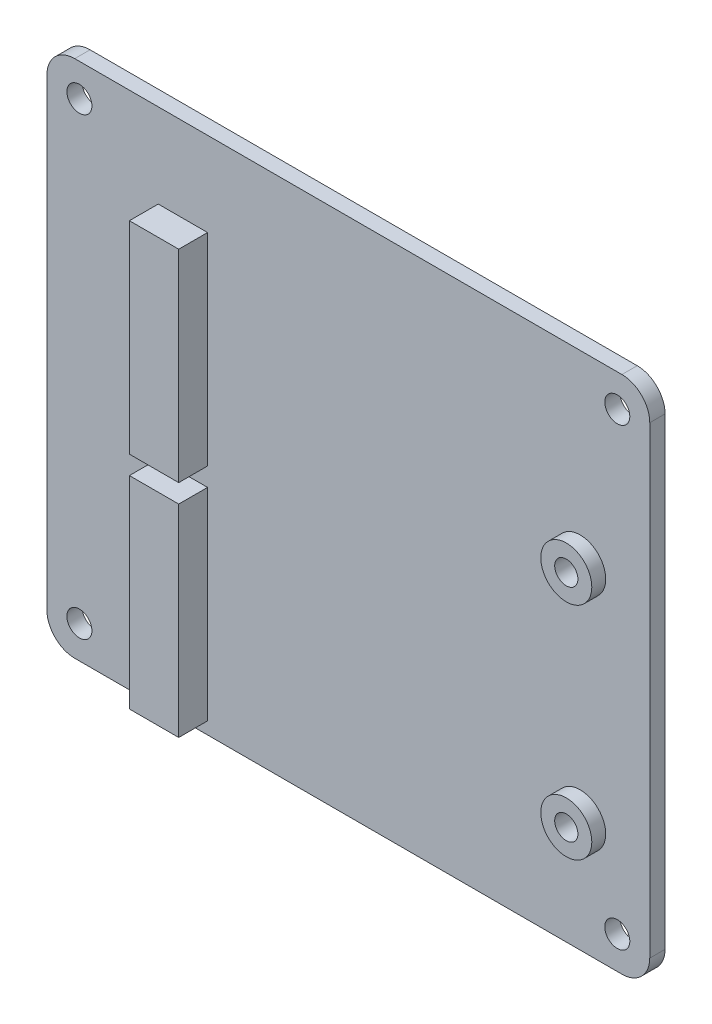
SolidWorks part; units mm, degrees
ref_plane "前视基准面" through (0, 0, 0) normal (0, 0, 1) x (1, 0, 0)
ref_plane "上视基准面" through (0, 0, 0) normal (0, 1, 0) x (1, 0, 0)
ref_plane "右视基准面" through (0, 0, 0) normal (1, 0, 0) x (0, 0, -1)
other "Configuration Table"
sketch "草图1" plane through (23.5903, 87.7411, -201.3211) normal (0, 0, 1) x (1, 0, 0)
  line L1 (-93.3542, 91.4857) -> (-34.3542, 91.4857)
  line L2 (-96.3542, 88.4857) -> (-96.3542, 38.4857)
  line L3 (-93.3542, 35.4857) -> (-34.3542, 35.4857)
  line L4 (-31.3542, 88.4857) -> (-31.3542, 38.4857)
  arc A0 (-34.3542, 91.4857) -> (-31.3542, 88.4857) centre (-34.3542, 88.4857) cw
  arc A1 (-34.3542, 35.4857) -> (-31.3542, 38.4857) centre (-34.3542, 38.4857) ccw
  arc A2 (-96.3542, 38.4857) -> (-93.3542, 35.4857) centre (-93.3542, 38.4857) ccw
  arc A3 (-93.3542, 91.4857) -> (-96.3542, 88.4857) centre (-93.3542, 88.4857) ccw
  point P6 (-31.3542, 91.4857)
  point P11 (-96.3542, 35.4857)
  point P14 (-96.3542, 91.4857)
  dimension "D3" = 3
  dimension "D1" = 65
  dimension "D2" = 56
extrude "凸台-拉伸1" add sketch "草图1" along normal blind 1.65
sketch "草图2" plane through (0, 0, -199.6711) normal (0, 0, 1) x (1, 0, 0)
  line L1 (-10.7639, 179.2268) -> (-69.7639, 179.2268) construction
  line L2 (-69.7639, 123.2268) -> (-10.7639, 123.2268) construction
  line L3 (-7.7639, 126.2268) -> (-7.7639, 176.2268) construction
  line L4 (-72.7639, 176.2268) -> (-72.7639, 126.2268) construction
  circle A0 centre (-69.2639, 175.7268) radius 1.35
  circle A1 centre (-11.2639, 175.7268) radius 1.35
  circle A2 centre (-69.2639, 126.7268) radius 1.35
  circle A3 centre (-11.2639, 126.7268) radius 1.35
  dimension "D1" = 2.7
  dimension "D2" = 3.5
  dimension "D3" = 3.5
  dimension "D4" = 3.5
  dimension "D5" = 3.5
extrude "切除-拉伸1" cut sketch "草图2" against normal blind 1.65
sketch "草图3" plane through (0, 0, -199.6711) normal (0, 0, 1) x (1, 0, 0)
  line L0 (-69.7639, 123.2268) -> (-10.7639, 123.2268) construction
  line L1 (-60.7639, 170.1468) -> (-55.4439, 170.1468)
  line L2 (-60.7639, 170.1468) -> (-60.7639, 148.3468)
  line L3 (-60.7639, 148.3468) -> (-55.4439, 148.3468)
  line L4 (-55.4439, 170.1468) -> (-55.4439, 148.3468)
  line L5 (-60.7639, 146.3468) -> (-55.4439, 146.3468)
  line L6 (-60.7639, 146.3468) -> (-60.7639, 124.5468)
  line L7 (-60.7639, 124.5468) -> (-55.4439, 124.5468)
  line L8 (-55.4439, 146.3468) -> (-55.4439, 124.5468)
  line L9 (-72.7639, 176.2268) -> (-72.7639, 126.2268) construction
  dimension "D1" = 21.8
  dimension "D2" = 5.32
  dimension "D3" = 1.32
  dimension "D4" = 2
  dimension "D5" = 12
extrude "凸台-拉伸2" add sketch "草图3" along normal blind 3.11
sketch "草图4" plane through (0, 0, -199.6711) normal (0, 0, 1) x (1, 0, 0)
  line L0 (-55.4439, 148.3468) -> (-55.4439, 170.1468) construction
  line L1 (-55.4439, 124.5468) -> (-55.4439, 146.3468) construction
  line L2 (-7.7639, 126.2268) -> (-7.7639, 176.2268) construction
  circle A0 centre (-15.2639, 135.4468) radius 2.75
  circle A1 centre (-15.2639, 159.2468) radius 2.75
  point P6 (-55.4439, 159.2468)
  point P10 (-55.4439, 135.4468)
  dimension "D1" = 5.5
  dimension "D2" = 7.5
extrude "凸台-拉伸3" add sketch "草图4" along normal blind 1.5
sketch "草图5" plane through (0, 0, -198.1711) normal (0, 0, 1) x (1, 0, 0)
  circle A0 centre (-15.2639, 159.2468) radius 1.25
  circle A1 centre (-15.2639, 135.4468) radius 1.25
  dimension "D1" = 2.5
extrude "切除-拉伸2" cut sketch "草图5" against normal up to next
